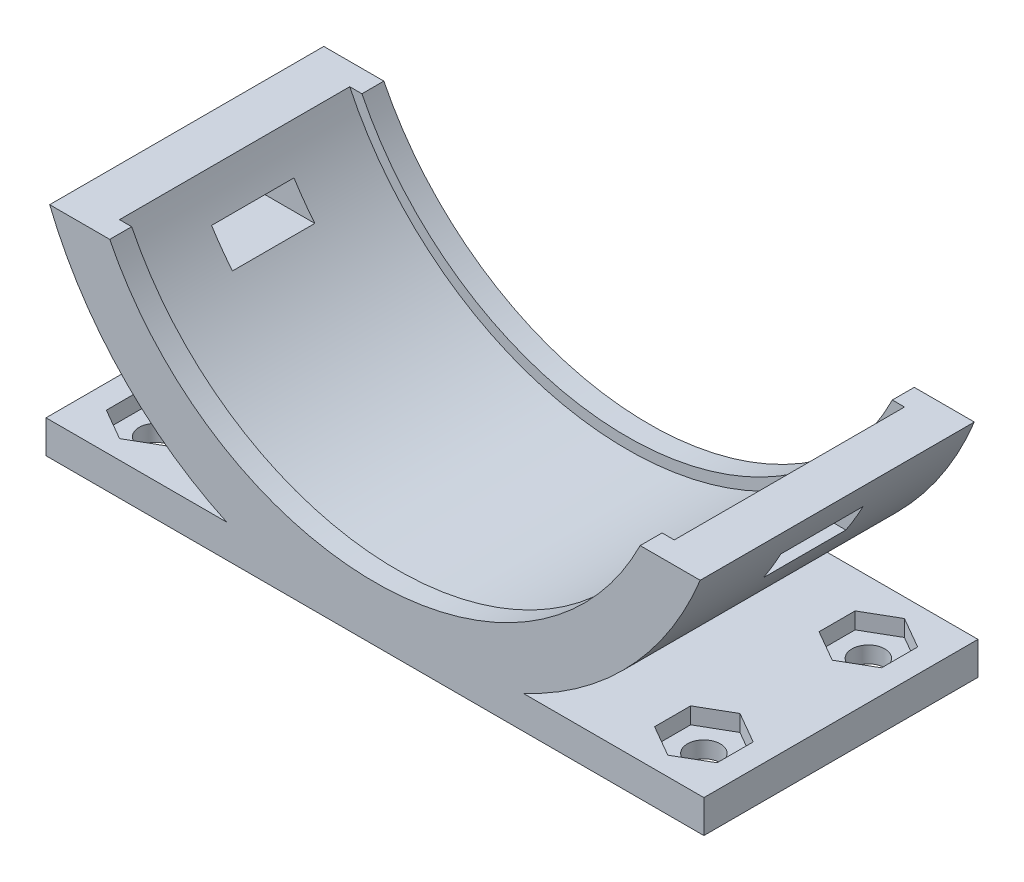
SolidWorks part; units mm, degrees
ref_plane "前视基准面" through (0, 0, 0) normal (0, 0, 1) x (1, 0, 0)
ref_plane "上视基准面" through (0, 0, 0) normal (0, 1, 0) x (1, 0, 0)
ref_plane "右视基准面" through (0, 0, 0) normal (1, 0, 0) x (0, 0, -1)
sketch "草图1" plane through (0, 0, 0) normal (0, 0, 1) x (1, 0, 0)
  line L0 (30, -32) -> (-30, -32)
  line L1 (-30, -32) -> (-30, -29)
  line L2 (-30, -29) -> (-13.5277, -29)
  line L3 (0, 0) -> (0, -7.1219) construction
  line L4 (30, -29) -> (13.5277, -29)
  line L5 (30, -32) -> (30, -29)
  line L6 (-29.6648, -12) -> (-24.1868, -12)
  line L7 (24.1868, -12) -> (29.6648, -12)
  arc A0 (-24.1868, -12) -> (24.1868, -12) centre (0, 0) ccw
  arc A1 (-29.6648, -12) -> (-13.5277, -29) centre (0, 0) ccw
  arc A2 (13.5277, -29) -> (29.6648, -12) centre (0, 0) ccw
  point P12 (0, -32)
  dimension "D1" = 54
  dimension "D2" = 5
  dimension "D3" = 30
  dimension "D4" = 3
  dimension "D5" = 20
extrude "凸台-拉伸1" add sketch "草图1" along normal blind 25
sketch "草图2" plane through (0, 0, 0) normal (1, 0, 0) x (0, 0, -1)
  line L0 (-25, -12) -> (0, -12) construction
  line L1 (-16.257, -15) -> (-8.743, -15)
  line L2 (-16.257, -15) -> (-16.257, -17.6458)
  line L3 (-16.257, -17.6458) -> (-8.743, -17.6458)
  line L4 (-8.743, -15) -> (-8.743, -17.6458)
  line L5 (-16.257, -15) -> (-8.743, -17.6458) construction
  line L6 (-16.257, -17.6458) -> (-8.743, -15) construction
  point P0 (-12.5, -16.3229)
  point P5 (-12.5, -14.9836)
  dimension "D1" = 3
extrude "切除-拉伸1" cut sketch "草图2" against normal blind 54 and the other way blind 109
sketch "草图3" plane through (0, -32, 0) normal (0, -1, 0) x (1, 0, 0)
  line L0 (-30, 25) -> (30, 25) construction
  line L1 (-30, 25) -> (-30, 0) construction
  line L2 (30, 25) -> (30, 0) construction
  line L3 (-30, 12.5) -> (-25.6431, 12.5) construction
  circle A0 centre (-25, 20) radius 1.5
  circle A1 centre (25, 20) radius 1.5
  circle A2 centre (25, 5) radius 1.5
  circle A3 centre (-25, 5) radius 1.5
  dimension "D1" = 3
  dimension "D2" = 5
  dimension "D3" = 5
  dimension "D4" = 3
  dimension "D5" = 5
  dimension "D6" = 5
extrude "切除-拉伸2" cut sketch "草图3" against normal blind 7
sketch "草图4" plane through (0, 0, 25) normal (0, 0, 1) x (1, 0, 0)
  line L0 (24.1868, -12) -> (25.2982, -12)
  line L1 (-24.1868, -12) -> (-25.2982, -12)
  arc A0 (-24.1868, -12) -> (24.1868, -12) centre (0, 0) ccw construction
  arc A1 (-24.1868, -12) -> (24.1868, -12) centre (0, 0) ccw
  arc A3 (-25.2982, -12) -> (25.2982, -12) centre (0, 0) ccw
extrude "切除-拉伸3" cut sketch "草图4" against normal blind 21 from offset 2 offset against normal yes
sketch "草图5" plane through (0, -29, 0) normal (0, 1, 0) x (1, 0, 0)
  line L0 (-30, -12.5) -> (0, -12.5) construction
  line L1 (-25, -23.2909) -> (-22.15, -21.6454)
  line L2 (-22.15, -21.6454) -> (-22.15, -18.3546)
  line L3 (-22.15, -18.3546) -> (-25, -16.7091)
  line L4 (-25, -16.7091) -> (-27.85, -18.3546)
  line L5 (-27.85, -18.3546) -> (-27.85, -21.6454)
  line L6 (-27.85, -21.6454) -> (-25, -23.2909)
  line L7 (-30, -25) -> (-30, 0) construction
  line L8 (0, -12.5) -> (0, 0) construction
  line L9 (27.85, -21.6454) -> (25, -23.2909)
  line L10 (27.85, -18.3546) -> (27.85, -21.6454)
  line L11 (25, -16.7091) -> (27.85, -18.3546)
  line L12 (22.15, -18.3546) -> (25, -16.7091)
  line L13 (22.15, -21.6454) -> (22.15, -18.3546)
  line L14 (25, -23.2909) -> (22.15, -21.6454)
  line L15 (25, -1.7091) -> (22.15, -3.3546)
  line L16 (22.15, -3.3546) -> (22.15, -6.6454)
  line L17 (22.15, -6.6454) -> (25, -8.2909)
  line L18 (25, -8.2909) -> (27.85, -6.6454)
  line L19 (27.85, -6.6454) -> (27.85, -3.3546)
  line L20 (27.85, -3.3546) -> (25, -1.7091)
  line L21 (-27.85, -3.3546) -> (-25, -1.7091)
  line L22 (-27.85, -6.6454) -> (-27.85, -3.3546)
  line L23 (-25, -8.2909) -> (-27.85, -6.6454)
  line L24 (-22.15, -6.6454) -> (-25, -8.2909)
  line L25 (-22.15, -3.3546) -> (-22.15, -6.6454)
  line L26 (-25, -1.7091) -> (-22.15, -3.3546)
  circle A0 centre (-25, -20) radius 2.85 construction
  circle A2 centre (25, -20) radius 2.85 construction
  circle A3 centre (25, -5) radius 2.85 construction
  circle A4 centre (-25, -5) radius 2.85 construction
  dimension "D1" = 5.7
extrude "切除-拉伸4" cut sketch "草图5" against normal blind 1.5
